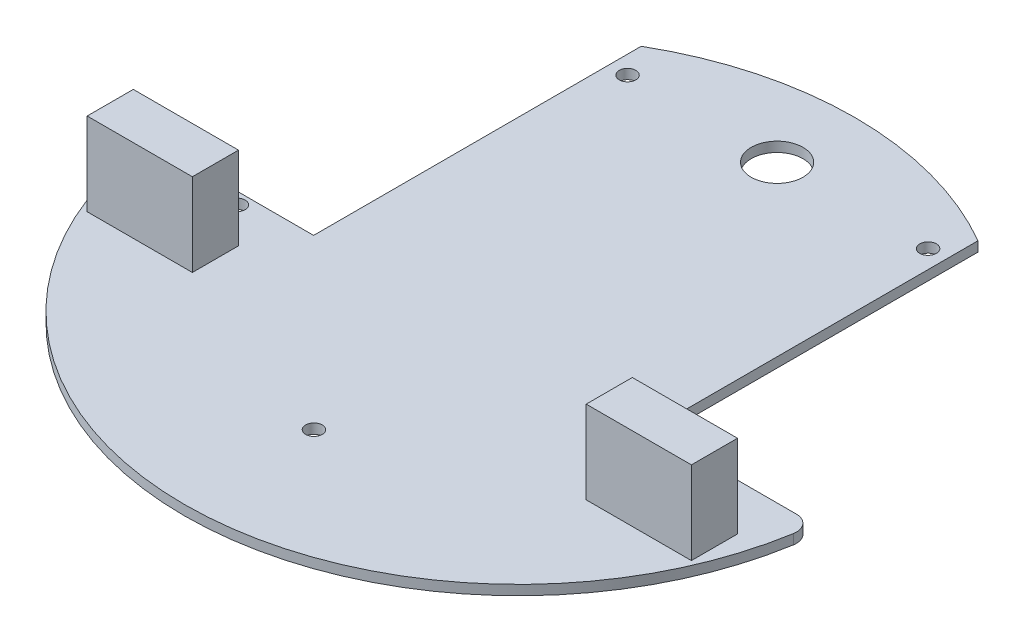
SolidWorks part; units mm, degrees
material "ABS"
ref_plane "Front Plane" through (0, 0, 0) normal (0, 0, 1) x (1, 0, 0)
ref_plane "Top Plane" through (0, 0, 0) normal (0, 1, 0) x (1, 0, 0)
ref_plane "Right Plane" through (0, 0, 0) normal (1, 0, 0) x (0, 0, -1)
sketch "Sketch1" plane through (0, 0, 0) normal (0, 1, 0) x (1, 0, 0)
  line L1 (-18, -10) -> (18, -10)
  line L2 (-18, -10) -> (-18, 10)
  line L3 (-18, 10) -> (18, 10)
  line L4 (18, -10) -> (18, 10)
  line L5 (-18, -10) -> (18, 10) construction
  line L6 (-18, 10) -> (18, -10) construction
  point P0 (0, 0)
  dimension "D1" = 36
  dimension "D2" = 20
extrude "Boss-Extrude1" add sketch "Sketch1" along normal blind 1.9
sketch "Sketch3" plane through (0, 0, 0) normal (0, -1, 0) x (1, 0, 0)
  line L0 (0, 0) -> (0, 52.4373) construction
  line L1 (37.5, -26.7252) -> (-37.5, -26.7252) construction
  line L2 (37.5, -26.7252) -> (32.5, -26.7252)
  line L3 (0, 0) -> (0, -36.2287) construction
  line L4 (-37.5, -26.7252) -> (-32.5, -26.7252)
  line L5 (32.5, -26.7252) -> (32.5, 33.2748)
  line L6 (-32.5, -26.7252) -> (-32.5, 33.2748)
  line L7 (32.5, 33.2748) -> (60.6723, 33.2748)
  line L9 (-32.5, 33.2748) -> (-60.6723, 33.2748)
  arc A0 (37.5, -26.7252) -> (-37.5, -26.7252) centre (0, 26.2187) cw
  arc A1 (-34.4904, -36.825) -> (34.4886, -36.825) centre (-0.0009, 26.4572) ccw construction
  arc A2 (68.1909, 19.7187) -> (51.8431, 70.9907) centre (0, 26.2187) ccw construction
  arc A3 (63.6319, 36.7654) -> (-63.6319, 36.7654) centre (0, 26.2187) ccw
  circle A4 centre (0, 26.2187) radius 72.5 construction
  arc A5 (-60.6723, 33.2748) -> (-63.6319, 36.7654) centre (-60.6723, 36.2748) cw
  arc A6 (60.6723, 33.2748) -> (63.6319, 36.7654) centre (60.6723, 36.2748) ccw
  point P7 (0, 26.2187)
  point P20 (-64.1129, 33.2748)
  point P26 (64.1129, 33.2748)
  dimension "D1" = 4
  dimension "D3" = 5
  dimension "D4" = 60
  dimension "D5" = 3
  dimension "D6" = 7.0562
  dimension "D2" = 65
extrude "Boss-Extrude2" add sketch "Sketch3" against normal blind 1.9
sketch "Sketch4" plane through (0, 1.9, 0) normal (0, 1, 0) x (1, 0, 0)
  line L0 (-32.5, 26.7252) -> (-32.5, 34.1947)
  line L1 (-32.5, 34.1947) -> (-40.4421, 34.1947)
  line L2 (-40.4421, 34.1947) -> (-37.5, 26.7252)
  line L3 (-37.5, 26.7252) -> (-32.5, 26.7252)
  line L4 (0, 0) -> (0, 49.3906) construction
  line L5 (37.5, 26.7252) -> (32.5, 26.7252)
  line L6 (40.4421, 34.1947) -> (37.5, 26.7252)
  line L7 (32.5, 34.1947) -> (40.4421, 34.1947)
  line L8 (32.5, 26.7252) -> (32.5, 34.1947)
  arc A0 (37.5, 26.7252) -> (-37.5, 26.7252) centre (0, -26.2187) ccw construction
extrude "Cut-Extrude1" cut sketch "Sketch4" against normal blind 10
sketch "Sketch5" plane through (0, 1.9, 0) normal (0, 1, 0) x (1, 0, 0)
  line L0 (0, 0) -> (0, 38.6605) construction
  circle A0 centre (0, 23.6605) radius 5
  arc A1 (32.5, 29.9334) -> (-32.5, 29.9334) centre (0, -26.2187) ccw construction
  dimension "D1" = 10
  dimension "D2" = 15
extrude "Cut-Extrude2" cut sketch "Sketch5" against normal up to surface (1.9 mm away) up to face at (0, 0, 23.8273)
sketch "Sketch6" plane through (0, 1.9, 0) normal (0, 1, 0) x (1, 0, 0)
  line L0 (0, 38.6605) -> (0, -90.7187) construction
  line L1 (-45, -35.5743) -> (45, -35.5743) construction
  line L2 (-29, 23.8048) -> (29, 23.8048) construction
  line L3 (-45, -31.5743) -> (-45, -49.6893) construction
  line L4 (-50, -31.5743) -> (-40, -31.5743) construction
  arc A0 (32.5, 29.9334) -> (-32.5, 29.9334) centre (0, -26.2187) ccw construction
  arc A1 (-63.6319, -36.7654) -> (63.6319, -36.7654) centre (0, -26.2187) ccw construction
  circle A2 centre (0, -65.7187) radius 1.6
  circle A3 centre (-45, -35.5743) radius 1.6
  circle A4 centre (45, -35.5743) radius 1.6
  circle A5 centre (-29, 23.8048) radius 1.6
  circle A6 centre (29, 23.8048) radius 1.6
  dimension "D1" = 25
  dimension "D2" = 3.2
  dimension "D3" = 4
  dimension "D5" = 58
extrude "Cut-Extrude3" cut sketch "Sketch6" against normal up to surface (1.9 mm away) up to face at (0, 0, -28.6605)
sketch "Esquisse1" plane through (0, 1.9, 0) normal (0, 1, 0) x (1, 0, 0)
  line L0 (0, 0) -> (0, -58.0938) construction
  line L1 (58.3, -42.2748) -> (38, -42.2748)
  line L2 (58.3, -42.2748) -> (58.3, -51.1748)
  line L3 (58.3, -51.1748) -> (38, -51.1748)
  line L4 (38, -42.2748) -> (38, -51.1748)
  line L5 (-38, -42.2748) -> (-38, -51.1748)
  line L6 (-58.3, -51.1748) -> (-38, -51.1748)
  line L7 (-58.3, -42.2748) -> (-58.3, -51.1748)
  line L8 (-58.3, -42.2748) -> (-38, -42.2748)
  line L10 (32.5, -33.2748) -> (60.6723, -33.2748) construction
  dimension "D1" = 20.3
  dimension "D2" = 38
  dimension "D3" = 9
  dimension "D4" = 8.9
extrude "Boss.-Extru.1" add sketch "Esquisse1" along normal blind 16
